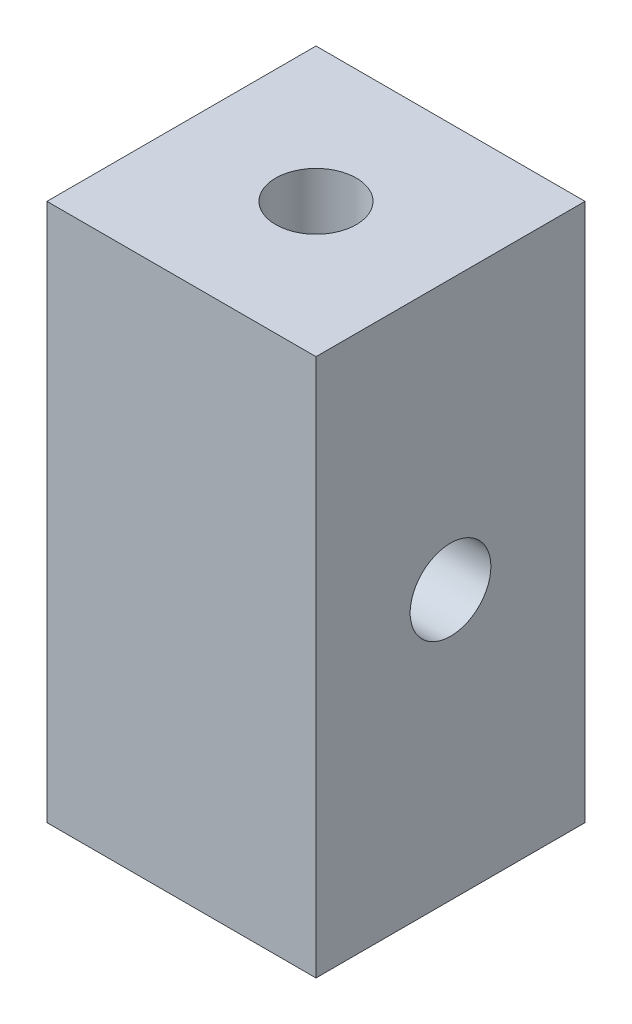
SolidWorks part; units mm, degrees
ref_plane "Front Plane" through (0, 0, 0) normal (0, 0, 1) x (1, 0, 0)
ref_plane "Top Plane" through (0, 0, 0) normal (0, 1, 0) x (1, 0, 0)
ref_plane "Right Plane" through (0, 0, 0) normal (1, 0, 0) x (0, 0, -1)
sketch "Sketch1" plane through (0, 0, 0) normal (0, 1, 0) x (1, 0, 0)
  line L1 (-5, -5) -> (5, -5)
  line L2 (-5, -5) -> (-5, 5)
  line L3 (-5, 5) -> (5, 5)
  line L4 (5, -5) -> (5, 5)
  line L5 (-5, -5) -> (5, 5) construction
  line L6 (-5, 5) -> (5, -5) construction
  circle A0 centre (0, 0) radius 1.5
  dimension "D1" = 3
  dimension "D2" = 5
  dimension "D3" = 5
extrude "Boss-Extrude1" add sketch "Sketch1" along normal blind 20 contours L2 L3 L4 L1
sketch "Sketch4" plane through (5, 0, 0) normal (1, 0, 0) x (0, 0, -1)
  line L1 (-5, 20) -> (-5, 0) construction
  circle A0 centre (0, 10) radius 1.5
  point P6 (-5, 10)
  dimension "D1" = 3
  dimension "D2" = 0
extrude "Cut-Extrude2" cut sketch "Sketch4" against normal through all
sketch "Sketch5" plane through (0, 20, 0) normal (0, 1, 0) x (1, 0, 0)
  circle A0 centre (0, 0) radius 1.5
  dimension "D1" = 3
extrude "Cut-Extrude3" cut sketch "Sketch5" against normal through all
